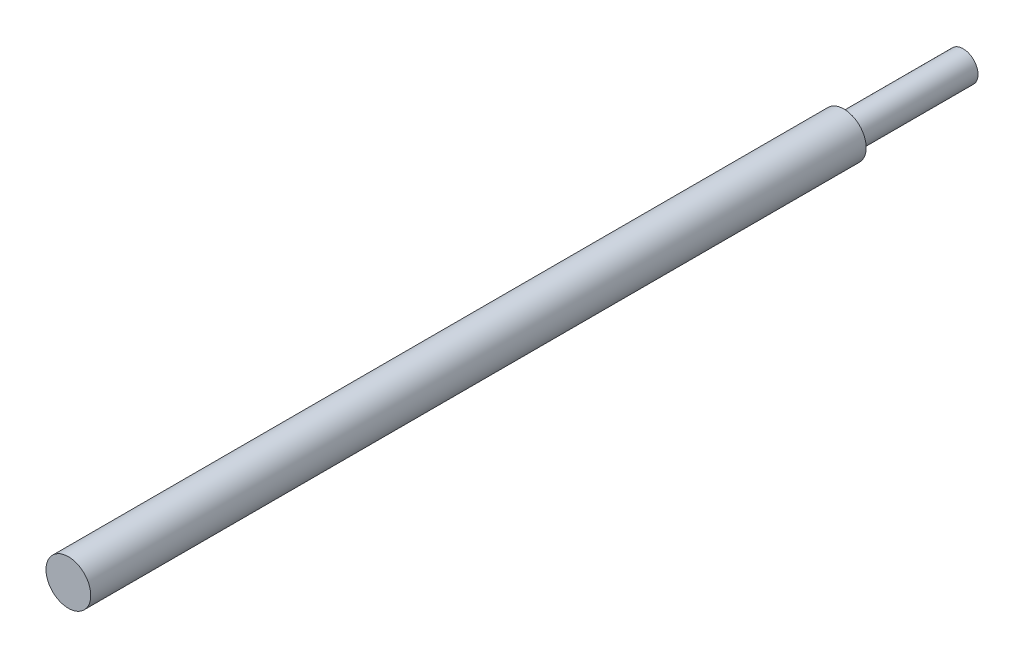
SolidWorks part; units mm, degrees
ref_plane "前视基准面" through (0, 0, 0) normal (0, 0, 1) x (1, 0, 0)
ref_plane "上视基准面" through (0, 0, 0) normal (0, 1, 0) x (1, 0, 0)
ref_plane "右视基准面" through (0, 0, 0) normal (1, 0, 0) x (0, 0, -1)
sketch "草图1" plane through (0, 0, 0) normal (0, 0, 1) x (1, 0, 0)
  circle A0 centre (0, 0) radius 7.5
  dimension "D1" = 15
extrude "凸台-拉伸1" add sketch "草图1" along normal blind 300
sketch "草图2" plane through (0, 0, 0) normal (0, 0, -1) x (-1, 0, 0)
  circle A0 centre (0, 0) radius 5
  dimension "D1" = 10
extrude "切除-拉伸1" cut sketch "草图2" against normal blind 40 flip side to cut
